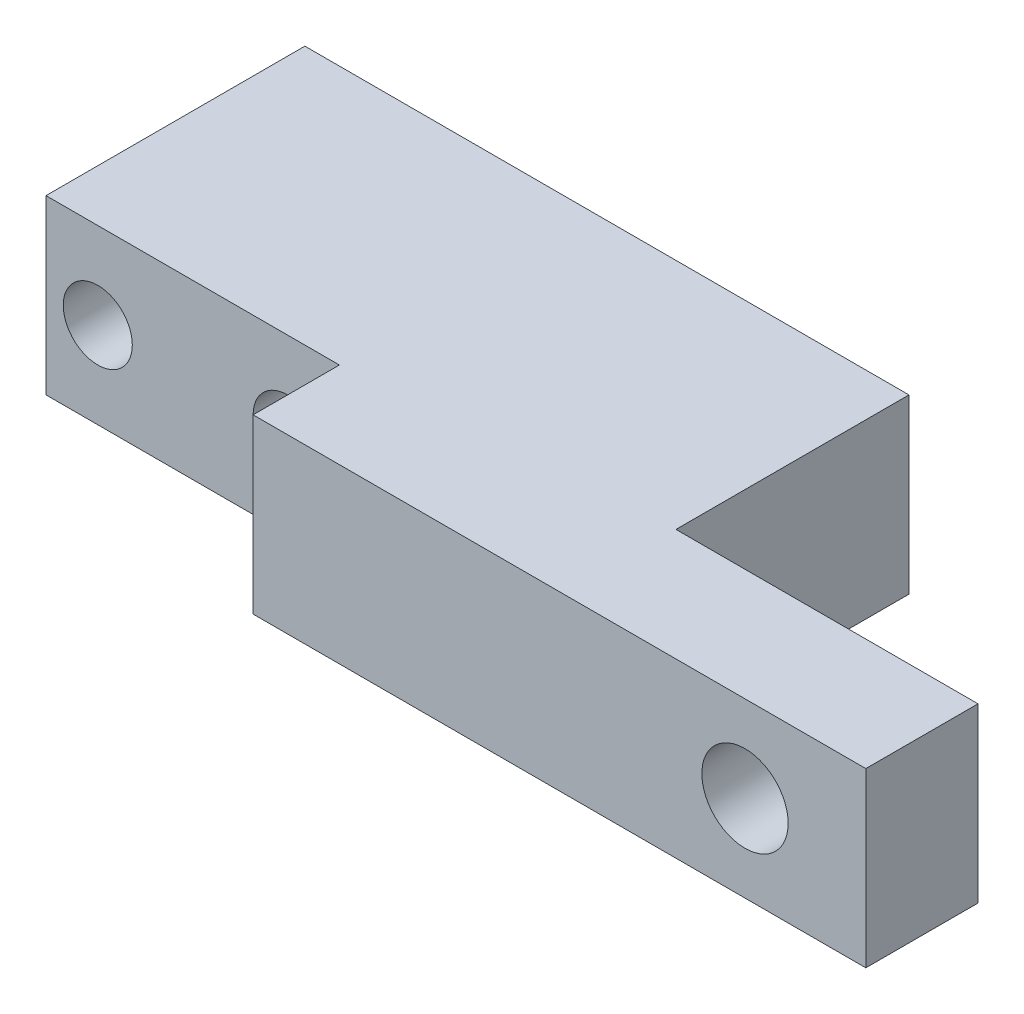
SolidWorks part; units mm, degrees
ref_plane "Plan de face" through (0, 0, 0) normal (0, 0, 1) x (1, 0, 0)
ref_plane "Plan de dessus" through (0, 0, 0) normal (0, 1, 0) x (1, 0, 0)
ref_plane "Plan de droite" through (0, 0, 0) normal (1, 0, 0) x (0, 0, -1)
sketch "Esquisse1" plane through (0, 0, 0) normal (0, 0, 1) x (1, 0, 0)
  line L0 (0, 0) -> (52.5, 0)
  line L1 (52.5, 0) -> (52.5, -10)
  line L2 (52.5, -10) -> (0, -10)
  line L3 (0, -10) -> (0, 0)
extrude "Extrusion1" add sketch "Esquisse1" along normal blind 20
sketch "Esquisse2" plane through (0, 0, 0) normal (0, 1, 0) x (1, 0, 0)
  line L0 (0, -20) -> (17, -20)
  line L3 (52.5, -20) -> (0, -20) construction
  line L4 (17, -20) -> (17, -15)
  line L5 (17, -15) -> (0, -15)
  line L6 (52.5, 0) -> (52.5, -13.5)
  line L8 (35, -13.5) -> (52.5, -13.5)
  line L9 (35, -13.5) -> (35, 0)
  line L10 (52.5, 0) -> (0, 0) construction
  line L11 (35, 0) -> (52.5, 0)
  line L12 (0, -20) -> (0, 0) construction
  line L13 (0, -15) -> (0, -20)
  dimension "D1" = 13.5
sketch "Esquisse3" plane through (0, 0, 20) normal (0, 0, 1) x (1, 0, 0)
  circle A0 centre (3, -5) radius 2
  circle A1 centre (14, -5) radius 2
extrude "Extrusion3" cut sketch "Esquisse3" against normal through all
sketch "Esquisse4" plane through (0, 0, 20) normal (0, 0, 1) x (1, 0, 0)
  circle A0 centre (45.5, -5) radius 2.5
extrude "Extrusion4" cut sketch "Esquisse4" against normal blind 20
extrude "Extrusion5" cut sketch "Esquisse2" against normal blind 20
